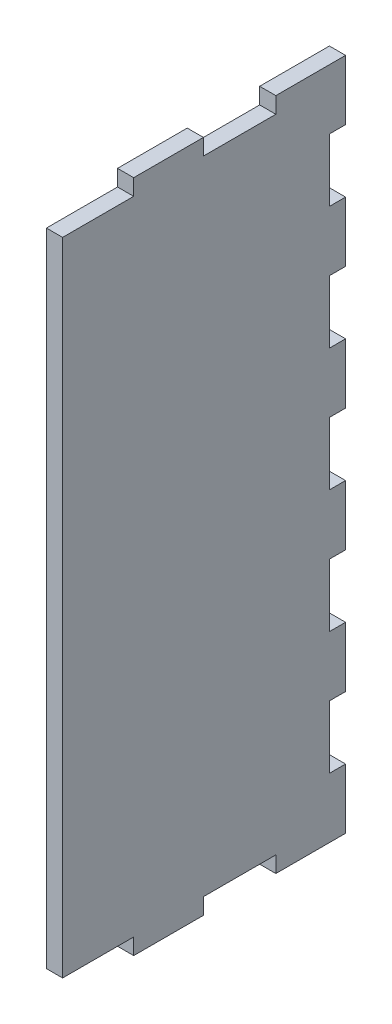
SolidWorks part; units mm, degrees
material "Plywood"
ref_plane "Front Plane" through (0, 0, 0) normal (0, 0, 1) x (1, 0, 0)
ref_plane "Top Plane" through (0, 0, 0) normal (0, 1, 0) x (1, 0, 0)
ref_plane "Right Plane" through (0, 0, 0) normal (1, 0, 0) x (0, 0, -1)
ref_plane "Plane1" through (330, 0, 0) normal (1, 0, 0) x (0, 0, -1)
sketch "Sketch1" plane through (330, 0, 0) normal (1, 0, 0) x (0, 0, -1)
  line L0 (-52.75, 244) -> (-52.75, 250)
  line L1 (-52.75, 250) -> (-78.625, 250)
  line L2 (-78.625, 250) -> (-78.625, 244)
  line L3 (-78.625, 244) -> (-105, 244)
  line L4 (-105, 244) -> (-105, 6)
  line L5 (-105, 6) -> (-78.625, 6)
  line L6 (-78.625, 6) -> (-78.625, 0)
  line L7 (-78.625, 0) -> (-52.75, 0)
  line L8 (-52.75, 0) -> (-52.75, 6)
  line L9 (-52.75, 6) -> (-25.875, 6)
  line L10 (-25.875, 6) -> (-25.875, 0)
  line L11 (-25.875, 0) -> (0, 0)
  line L12 (0, 0) -> (0, 22.2727)
  line L13 (0, 22.2727) -> (-6, 22.2727)
  line L14 (-6, 22.2727) -> (-6, 45.5455)
  line L15 (-6, 45.5455) -> (0, 45.5455)
  line L16 (0, 45.5455) -> (0, 67.8182)
  line L17 (0, 67.8182) -> (-6, 67.8182)
  line L18 (-6, 67.8182) -> (-6, 91.0909)
  line L19 (-6, 91.0909) -> (0, 91.0909)
  line L20 (0, 91.0909) -> (0, 113.3636)
  line L21 (0, 113.3636) -> (-6, 113.3636)
  line L22 (-6, 113.3636) -> (-6, 136.6364)
  line L23 (-6, 136.6364) -> (0, 136.6364)
  line L24 (0, 136.6364) -> (0, 158.9091)
  line L25 (0, 158.9091) -> (-6, 158.9091)
  line L26 (-6, 158.9091) -> (-6, 182.1818)
  line L27 (-6, 182.1818) -> (0, 182.1818)
  line L28 (0, 182.1818) -> (0, 204.4545)
  line L29 (0, 204.4545) -> (-6, 204.4545)
  line L30 (-6, 204.4545) -> (-6, 227.7273)
  line L31 (-6, 227.7273) -> (0, 227.7273)
  line L32 (0, 227.7273) -> (0, 250)
  line L33 (0, 250) -> (-25.875, 250)
  line L34 (-25.875, 250) -> (-25.875, 244)
  line L35 (-25.875, 244) -> (-52.75, 244)
extrude "Boss-Extrude1" add sketch "Sketch1" against normal blind 6
